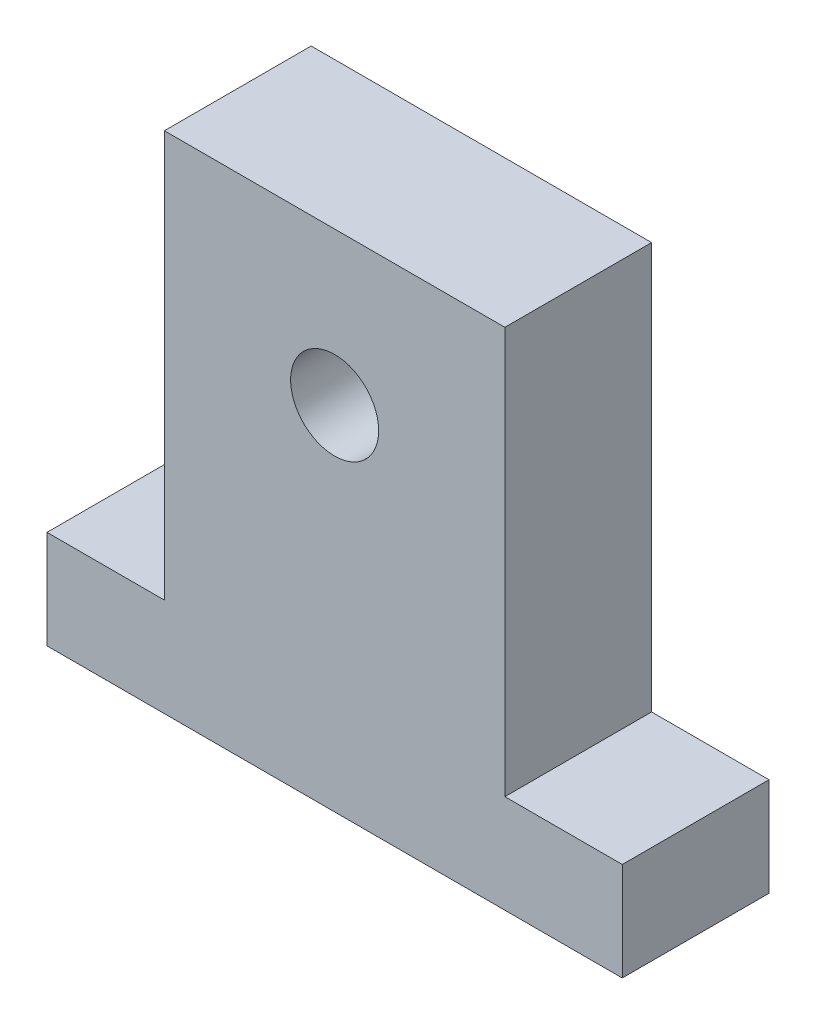
SolidWorks part; units mm, degrees
ref_plane "Alzado" through (0, 0, 0) normal (0, 0, 1) x (1, 0, 0)
ref_plane "Planta" through (0, 0, 0) normal (0, 1, 0) x (1, 0, 0)
ref_plane "Vista lateral" through (0, 0, 0) normal (1, 0, 0) x (0, 0, -1)
sketch "Croquis1" plane through (0, 0, 0) normal (0, 0, 1) x (1, 0, 0)
  line L0 (-19.6, 0) -> (-19.6, 6.7)
  line L1 (-19.6, 6.7) -> (-11.6, 6.7)
  line L2 (-11.6, 6.7) -> (-11.6, 34.4)
  line L3 (-11.6, 34.4) -> (11.6, 34.4)
  line L4 (11.6, 34.4) -> (11.6, 6.7)
  line L5 (11.6, 6.7) -> (19.6, 6.7)
  line L6 (19.6, 6.7) -> (19.6, 0)
  line L7 (19.6, 0) -> (-19.6, 0)
  circle A0 centre (0, 24) radius 3
  dimension "D9" = 24
  dimension "D1" = 23.2
  dimension "D2" = 8
  dimension "D3" = 8
  dimension "D4" = 11.6
  dimension "D5" = 6.7
  dimension "D6" = 6.7
  dimension "D7" = 0
  dimension "D8" = 27.7
extrude "Saliente-Extruir1" add sketch "Croquis1" along normal blind 10
